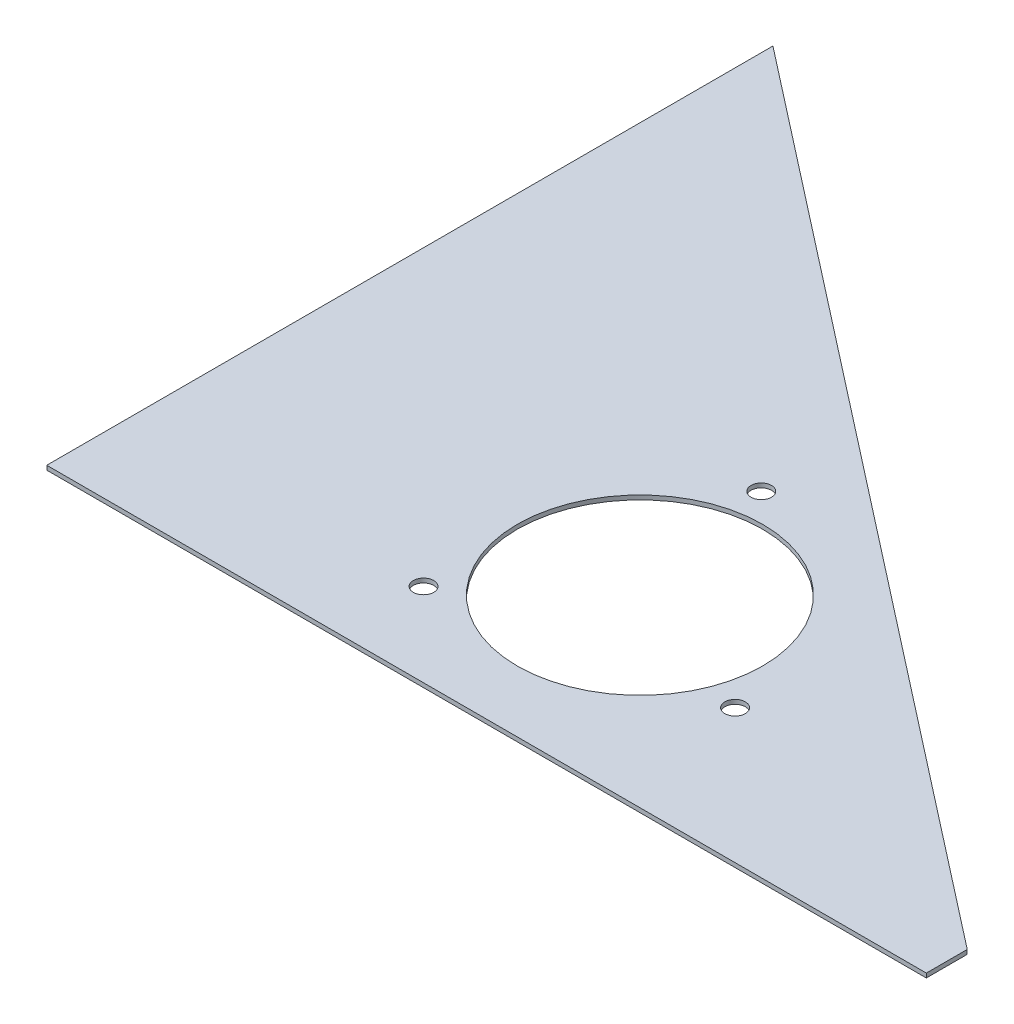
SolidWorks part; units mm, degrees
ref_plane "Front Plane" through (0, 0, 0) normal (0, 0, 1) x (1, 0, 0)
ref_plane "Top Plane" through (0, 0, 0) normal (0, 1, 0) x (1, 0, 0)
ref_plane "Right Plane" through (0, 0, 0) normal (1, 0, 0) x (0, 0, -1)
sketch "Sketch1" plane through (0, 0, 0) normal (0, 1, 0) x (1, 0, 0)
  line L0 (0, 450.85) -> (0, 0)
  line L1 (0, 0) -> (546.1, 0)
  line L2 (546.1, 0) -> (546.1, 25.4)
  line L3 (546.1, 25.4) -> (0, 450.85)
  dimension "D1" = 450.85
  dimension "D2" = 546.1
  dimension "D3" = 25.4
extrude "Boss-Extrude1" add sketch "Sketch1" along normal blind 2.6568
ref_plane "Plane1" through (220.1389, 0, -282.5663) normal (0.6146, 0, -0.7889) x (-0.7889, 0, -0.6146)
sketch "Sketch2" plane through (0, 0, 0) normal (0, -1, 0) x (1, 0, 0)
  line L0 (546.1, 0) -> (546.1, -25.4) construction
  line L1 (0, 0) -> (546.1, 0) construction
  circle A0 centre (254, -114.3) radius 76.2
  dimension "D1" = 152.4
  dimension "D2" = 292.1
  dimension "D3" = 114.3
extrude "Cut-Extrude1" cut sketch "Sketch2" against normal through all
sketch "Sketch3" plane through (0, 0, 0) normal (0, -1, 0) x (1, 0, 0)
  line L0 (0, -114.3) -> (431.9896, -114.3) construction
  line L8 (254, -252.9663) -> (254, 0) construction
  line L9 (546.1, -25.4) -> (0, -450.85) construction
  line L10 (0, 0) -> (546.1, 0) construction
  line L11 (0, -450.85) -> (0, 0) construction
  line L12 (254, -114.3) -> (621.1943, 12.1351) construction
  circle A0 centre (254, -114.3) radius 95.25 construction
  circle A1 centre (344.0606, -83.2896) radius 6.35
  circle A2 centre (235.8254, -207.8) radius 6.35
  circle A3 centre (182.1139, -51.8104) radius 6.35
  circle A4 centre (254, -114.3) radius 76.2 construction
  circle A5 centre (254, -114.3) radius 76.2 construction
  point P22 (254, -114.3)
  dimension "D1" = 190.5
  dimension "D3" = 12.7
  dimension "D2" = 19
  dimension "D4" = 3
extrude "Cut-Extrude2" cut sketch "Sketch3" against normal through all
